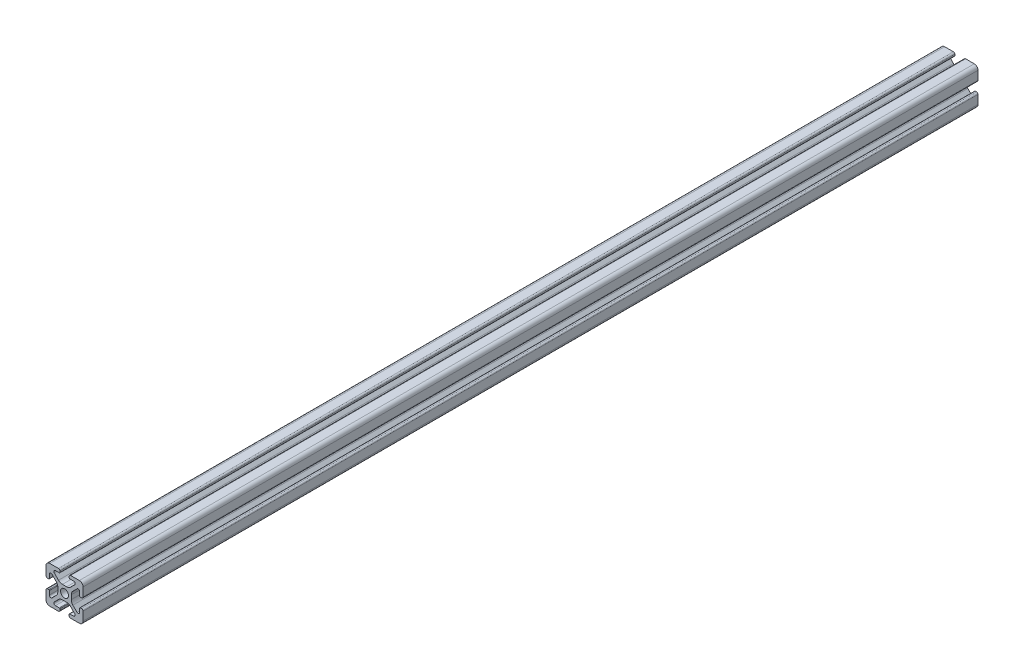
SolidWorks part; units mm, degrees
ref_plane "Front Plane" through (0, 0, 0) normal (0, 0, 1) x (1, 0, 0)
ref_plane "Top Plane" through (0, 0, 0) normal (0, 1, 0) x (1, 0, 0)
ref_plane "Right Plane" through (0, 0, 0) normal (1, 0, 0) x (0, 0, -1)
sketch "Sketch1" plane through (0, 0, 0) normal (0, 0, 1) x (1, 0, 0)
  line L2 (-9.9949, 7.9883) -> (-9.9949, 3.2893)
  line L3 (-7.9883, 9.9949) -> (-3.2893, 9.9949)
  line L4 (-2.5019, 9.2075) -> (-2.5019, 8.4963)
  line L5 (-2.8067, 8.1915) -> (-4.9149, 8.1915)
  line L6 (-5.5076, 6.7606) -> (-3.2528, 4.5058)
  line L7 (-6.7606, 5.5076) -> (-4.5058, 3.2528)
  line L8 (-8.1915, 4.9149) -> (-8.1915, 2.8067)
  line L9 (-8.4963, 2.5019) -> (-9.2075, 2.5019)
  line L11 (-1.1334, 3.6279) -> (1.1334, 3.6279)
  line L12 (-3.6279, 1.1334) -> (-3.6279, -1.1334)
  line L13 (8.4963, 2.5019) -> (9.2075, 2.5019)
  line L14 (8.1915, 4.9149) -> (8.1915, 2.8067)
  line L15 (9.9949, 7.9883) -> (9.9949, 3.2893)
  line L16 (7.9883, 9.9949) -> (3.2893, 9.9949)
  line L17 (2.5019, 9.2075) -> (2.5019, 8.4963)
  line L18 (2.8067, 8.1915) -> (4.9149, 8.1915)
  line L19 (3.6279, 1.1334) -> (3.6279, -1.1334)
  line L20 (5.5076, 6.7606) -> (3.2528, 4.5058)
  line L21 (6.7606, 5.5076) -> (4.5058, 3.2528)
  line L22 (-8.4963, -2.5019) -> (-9.2075, -2.5019)
  line L23 (-8.1915, -4.9149) -> (-8.1915, -2.8067)
  line L24 (-6.7606, -5.5076) -> (-4.5058, -3.2528)
  line L25 (-5.5076, -6.7606) -> (-3.2528, -4.5058)
  line L26 (-2.8067, -8.1915) -> (-4.9149, -8.1915)
  line L27 (-2.5019, -9.2075) -> (-2.5019, -8.4963)
  line L28 (-7.9883, -9.9949) -> (-3.2893, -9.9949)
  line L29 (-9.9949, -7.9883) -> (-9.9949, -3.2893)
  line L30 (9.9949, -7.9883) -> (9.9949, -3.2893)
  line L31 (7.9883, -9.9949) -> (3.2893, -9.9949)
  line L32 (2.5019, -9.2075) -> (2.5019, -8.4963)
  line L33 (2.8067, -8.1915) -> (4.9149, -8.1915)
  line L34 (5.5076, -6.7606) -> (3.2528, -4.5058)
  line L35 (6.7606, -5.5076) -> (4.5058, -3.2528)
  line L36 (8.1915, -4.9149) -> (8.1915, -2.8067)
  line L37 (8.4963, -2.5019) -> (9.2075, -2.5019)
  line L38 (-1.1334, -3.6279) -> (1.1334, -3.6279)
  circle A0 centre (0, 0) radius 2.1463
  arc A1 (-9.9949, 7.9883) -> (-7.9883, 9.9949) centre (-7.9883, 7.9883) cw
  arc A2 (-6.7606, 5.5076) -> (-8.1915, 4.9149) centre (-7.3533, 4.9149) ccw
  arc A3 (-4.9149, 8.1915) -> (-5.5076, 6.7606) centre (-4.9149, 7.3533) ccw
  arc A4 (-3.2893, 9.9949) -> (-2.5019, 9.2075) centre (-3.2893, 9.2075) cw
  arc A5 (-9.9949, 3.2893) -> (-9.2075, 2.5019) centre (-9.2075, 3.2893) ccw
  arc A6 (-8.1915, 2.8067) -> (-8.4963, 2.5019) centre (-8.4963, 2.8067) cw
  arc A7 (-2.5019, 8.4963) -> (-2.8067, 8.1915) centre (-2.8067, 8.4963) cw
  arc A8 (-1.1334, 3.6279) -> (-3.2528, 4.5058) centre (-1.1334, 6.6251) cw
  arc A9 (-3.6279, 1.1334) -> (-4.5058, 3.2528) centre (-6.6251, 1.1334) ccw
  arc A10 (8.1915, 2.8067) -> (8.4963, 2.5019) centre (8.4963, 2.8067) ccw
  arc A11 (9.9949, 3.2893) -> (9.2075, 2.5019) centre (9.2075, 3.2893) cw
  arc A12 (9.9949, 7.9883) -> (7.9883, 9.9949) centre (7.9883, 7.9883) ccw
  arc A13 (3.2893, 9.9949) -> (2.5019, 9.2075) centre (3.2893, 9.2075) ccw
  arc A14 (2.5019, 8.4963) -> (2.8067, 8.1915) centre (2.8067, 8.4963) ccw
  arc A15 (1.1334, 3.6279) -> (3.2528, 4.5058) centre (1.1334, 6.6251) ccw
  arc A16 (3.6279, 1.1334) -> (4.5058, 3.2528) centre (6.6251, 1.1334) cw
  arc A17 (6.7606, 5.5076) -> (8.1915, 4.9149) centre (7.3533, 4.9149) cw
  arc A18 (4.9149, 8.1915) -> (5.5076, 6.7606) centre (4.9149, 7.3533) cw
  arc A19 (-3.6279, -1.1334) -> (-4.5058, -3.2528) centre (-6.6251, -1.1334) cw
  arc A20 (-1.1334, -3.6279) -> (-3.2528, -4.5058) centre (-1.1334, -6.6251) ccw
  arc A21 (-2.5019, -8.4963) -> (-2.8067, -8.1915) centre (-2.8067, -8.4963) ccw
  arc A22 (-8.1915, -2.8067) -> (-8.4963, -2.5019) centre (-8.4963, -2.8067) ccw
  arc A23 (-9.9949, -3.2893) -> (-9.2075, -2.5019) centre (-9.2075, -3.2893) cw
  arc A24 (-3.2893, -9.9949) -> (-2.5019, -9.2075) centre (-3.2893, -9.2075) ccw
  arc A25 (-4.9149, -8.1915) -> (-5.5076, -6.7606) centre (-4.9149, -7.3533) cw
  arc A26 (-6.7606, -5.5076) -> (-8.1915, -4.9149) centre (-7.3533, -4.9149) cw
  arc A27 (-9.9949, -7.9883) -> (-7.9883, -9.9949) centre (-7.9883, -7.9883) ccw
  arc A28 (9.9949, -7.9883) -> (7.9883, -9.9949) centre (7.9883, -7.9883) cw
  arc A29 (6.7606, -5.5076) -> (8.1915, -4.9149) centre (7.3533, -4.9149) ccw
  arc A30 (4.9149, -8.1915) -> (5.5076, -6.7606) centre (4.9149, -7.3533) ccw
  arc A31 (3.2893, -9.9949) -> (2.5019, -9.2075) centre (3.2893, -9.2075) cw
  arc A32 (9.9949, -3.2893) -> (9.2075, -2.5019) centre (9.2075, -3.2893) ccw
  arc A33 (8.1915, -2.8067) -> (8.4963, -2.5019) centre (8.4963, -2.8067) cw
  arc A34 (2.5019, -8.4963) -> (2.8067, -8.1915) centre (2.8067, -8.4963) cw
  arc A35 (1.1334, -3.6279) -> (3.2528, -4.5058) centre (1.1334, -6.6251) cw
  arc A36 (3.6279, -1.1334) -> (4.5058, -3.2528) centre (6.6251, -1.1334) ccw
extrude "Boss-Extrude1" add sketch "Sketch1" along normal mid plane 482.6
sketch "Sketch2" plane through (0, 0, 241.3) normal (0, 0, 1) x (1, 0, 0)
  line L0 (9.9949, 3.2893) -> (9.9949, 7.9883) construction
  line L1 (-9.9949, -9.9949) -> (9.9949, -9.9949)
  line L2 (-9.9949, -9.9949) -> (-9.9949, 9.9949)
  line L3 (-9.9949, 9.9949) -> (9.9949, 9.9949)
  line L4 (9.9949, -9.9949) -> (9.9949, 9.9949)
  line L5 (-9.9949, -9.9949) -> (9.9949, 9.9949) construction
  line L6 (-9.9949, 9.9949) -> (9.9949, -9.9949) construction
  line L7 (7.9883, 9.9949) -> (3.2893, 9.9949) construction
  point P0 (0, 0)
extrude "Cut-Extrude1" [suppressed] cut sketch "Sketch2" against normal blind 279.4
